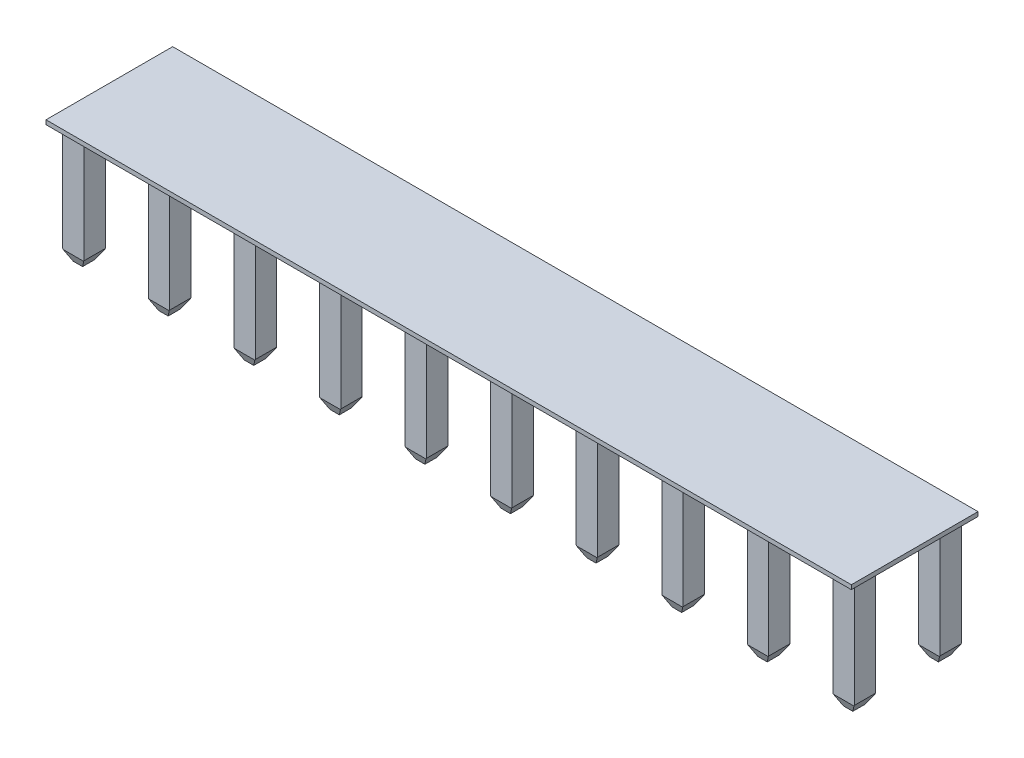
SolidWorks part; units mm, degrees
material "Pure Gold"
ref_plane "Front Plane" through (0, 0, 0) normal (0, 0, 1) x (1, 0, 0)
ref_plane "Top Plane" through (0, 0, 0) normal (0, 1, 0) x (1, 0, 0)
ref_plane "Right Plane" through (0, 0, 0) normal (1, 0, 0) x (0, 0, -1)
ref_plane "Plane1" through (0, 3.5306, 0) normal (0, -1, 0) x (1, 0, 0)
sketch "Sketch1" plane through (0, 3.5306, 0) normal (0, -1, 0) x (1, 0, 0)
  line L0 (-11.9507, 1.8796) -> (-11.9507, -1.8796)
  line L1 (-11.9507, -1.8796) -> (11.9507, -1.8796)
  line L2 (11.9507, -1.8796) -> (11.9507, 1.8796)
  line L3 (11.9507, 1.8796) -> (-11.9507, 1.8796)
extrude "Boss-Extrude1" add sketch "Sketch1" against normal blind 0.127
sketch "Sketch2" plane through (0, 3.5306, 0) normal (0, -1, 0) x (1, 0, 0)
  line L0 (11.7475, 0.9525) -> (11.1125, 0.9525)
  line L1 (11.1125, 0.9525) -> (11.1125, 1.5875)
  line L2 (11.1125, 1.5875) -> (11.7475, 1.5875)
  line L3 (11.7475, 1.5875) -> (11.7475, 0.9525)
extrude "Boss-Extrude2" add sketch "Sketch2" along normal blind 3.5306
sketch "Sketch3" plane through (0, 3.5306, 0) normal (0, -1, 0) x (1, 0, 0)
  line L0 (9.2075, 0.9525) -> (8.5725, 0.9525)
  line L1 (8.5725, 0.9525) -> (8.5725, 1.5875)
  line L2 (8.5725, 1.5875) -> (9.2075, 1.5875)
  line L3 (9.2075, 1.5875) -> (9.2075, 0.9525)
extrude "Boss-Extrude3" add sketch "Sketch3" along normal blind 3.5306
sketch "Sketch4" plane through (0, 3.5306, 0) normal (0, -1, 0) x (1, 0, 0)
  line L0 (6.6675, 0.9525) -> (6.0325, 0.9525)
  line L1 (6.0325, 0.9525) -> (6.0325, 1.5875)
  line L2 (6.0325, 1.5875) -> (6.6675, 1.5875)
  line L3 (6.6675, 1.5875) -> (6.6675, 0.9525)
extrude "Boss-Extrude4" add sketch "Sketch4" along normal blind 3.5306
sketch "Sketch5" plane through (0, 3.5306, 0) normal (0, -1, 0) x (1, 0, 0)
  line L0 (4.1275, 0.9525) -> (3.4925, 0.9525)
  line L1 (3.4925, 0.9525) -> (3.4925, 1.5875)
  line L2 (3.4925, 1.5875) -> (4.1275, 1.5875)
  line L3 (4.1275, 1.5875) -> (4.1275, 0.9525)
extrude "Boss-Extrude5" add sketch "Sketch5" along normal blind 3.5306
sketch "Sketch6" plane through (0, 3.5306, 0) normal (0, -1, 0) x (1, 0, 0)
  line L0 (1.5875, 0.9525) -> (0.9525, 0.9525)
  line L1 (0.9525, 0.9525) -> (0.9525, 1.5875)
  line L2 (0.9525, 1.5875) -> (1.5875, 1.5875)
  line L3 (1.5875, 1.5875) -> (1.5875, 0.9525)
extrude "Boss-Extrude6" add sketch "Sketch6" along normal blind 3.5306
sketch "Sketch7" plane through (0, 3.5306, 0) normal (0, -1, 0) x (1, 0, 0)
  line L0 (-0.9525, 0.9525) -> (-1.5875, 0.9525)
  line L1 (-1.5875, 0.9525) -> (-1.5875, 1.5875)
  line L2 (-1.5875, 1.5875) -> (-0.9525, 1.5875)
  line L3 (-0.9525, 1.5875) -> (-0.9525, 0.9525)
extrude "Boss-Extrude7" add sketch "Sketch7" along normal blind 3.5306
sketch "Sketch8" plane through (0, 3.5306, 0) normal (0, -1, 0) x (1, 0, 0)
  line L0 (-3.4925, 0.9525) -> (-4.1275, 0.9525)
  line L1 (-4.1275, 0.9525) -> (-4.1275, 1.5875)
  line L2 (-4.1275, 1.5875) -> (-3.4925, 1.5875)
  line L3 (-3.4925, 1.5875) -> (-3.4925, 0.9525)
extrude "Boss-Extrude8" add sketch "Sketch8" along normal blind 3.5306
sketch "Sketch9" plane through (0, 3.5306, 0) normal (0, -1, 0) x (1, 0, 0)
  line L0 (-6.0325, 0.9525) -> (-6.6675, 0.9525)
  line L1 (-6.6675, 0.9525) -> (-6.6675, 1.5875)
  line L2 (-6.6675, 1.5875) -> (-6.0325, 1.5875)
  line L3 (-6.0325, 1.5875) -> (-6.0325, 0.9525)
extrude "Boss-Extrude9" add sketch "Sketch9" along normal blind 3.5306
sketch "Sketch10" plane through (0, 3.5306, 0) normal (0, -1, 0) x (1, 0, 0)
  line L0 (-8.5725, 0.9525) -> (-9.2075, 0.9525)
  line L1 (-9.2075, 0.9525) -> (-9.2075, 1.5875)
  line L2 (-9.2075, 1.5875) -> (-8.5725, 1.5875)
  line L3 (-8.5725, 1.5875) -> (-8.5725, 0.9525)
extrude "Boss-Extrude10" add sketch "Sketch10" along normal blind 3.5306
sketch "Sketch11" plane through (0, 3.5306, 0) normal (0, -1, 0) x (1, 0, 0)
  line L0 (-11.7475, 1.5875) -> (-11.1125, 1.5875)
  line L1 (-11.1125, 1.5875) -> (-11.1125, 0.9525)
  line L2 (-11.1125, 0.9525) -> (-11.7475, 0.9525)
  line L3 (-11.7475, 0.9525) -> (-11.7475, 1.5875)
extrude "Boss-Extrude11" add sketch "Sketch11" along normal blind 3.5306
sketch "Sketch12" plane through (0, 3.5306, 0) normal (0, -1, 0) x (1, 0, 0)
  line L0 (11.7475, -1.5875) -> (11.1125, -1.5875)
  line L1 (11.1125, -1.5875) -> (11.1125, -0.9525)
  line L2 (11.1125, -0.9525) -> (11.7475, -0.9525)
  line L3 (11.7475, -0.9525) -> (11.7475, -1.5875)
extrude "Boss-Extrude12" add sketch "Sketch12" along normal blind 3.5306
sketch "Sketch13" plane through (0, 3.5306, 0) normal (0, -1, 0) x (1, 0, 0)
  line L0 (9.2075, -1.5875) -> (8.5725, -1.5875)
  line L1 (8.5725, -1.5875) -> (8.5725, -0.9525)
  line L2 (8.5725, -0.9525) -> (9.2075, -0.9525)
  line L3 (9.2075, -0.9525) -> (9.2075, -1.5875)
extrude "Boss-Extrude13" add sketch "Sketch13" along normal blind 3.5306
sketch "Sketch14" plane through (0, 3.5306, 0) normal (0, -1, 0) x (1, 0, 0)
  line L0 (6.6675, -1.5875) -> (6.0325, -1.5875)
  line L1 (6.0325, -1.5875) -> (6.0325, -0.9525)
  line L2 (6.0325, -0.9525) -> (6.6675, -0.9525)
  line L3 (6.6675, -0.9525) -> (6.6675, -1.5875)
extrude "Boss-Extrude14" add sketch "Sketch14" along normal blind 3.5306
sketch "Sketch15" plane through (0, 3.5306, 0) normal (0, -1, 0) x (1, 0, 0)
  line L0 (4.1275, -1.5875) -> (3.4925, -1.5875)
  line L1 (3.4925, -1.5875) -> (3.4925, -0.9525)
  line L2 (3.4925, -0.9525) -> (4.1275, -0.9525)
  line L3 (4.1275, -0.9525) -> (4.1275, -1.5875)
extrude "Boss-Extrude15" add sketch "Sketch15" along normal blind 3.5306
sketch "Sketch16" plane through (0, 3.5306, 0) normal (0, -1, 0) x (1, 0, 0)
  line L0 (1.5875, -1.5875) -> (0.9525, -1.5875)
  line L1 (0.9525, -1.5875) -> (0.9525, -0.9525)
  line L2 (0.9525, -0.9525) -> (1.5875, -0.9525)
  line L3 (1.5875, -0.9525) -> (1.5875, -1.5875)
extrude "Boss-Extrude16" add sketch "Sketch16" along normal blind 3.5306
sketch "Sketch17" plane through (0, 3.5306, 0) normal (0, -1, 0) x (1, 0, 0)
  line L0 (-0.9525, -1.5875) -> (-1.5875, -1.5875)
  line L1 (-1.5875, -1.5875) -> (-1.5875, -0.9525)
  line L2 (-1.5875, -0.9525) -> (-0.9525, -0.9525)
  line L3 (-0.9525, -0.9525) -> (-0.9525, -1.5875)
extrude "Boss-Extrude17" add sketch "Sketch17" along normal blind 3.5306
sketch "Sketch18" plane through (0, 3.5306, 0) normal (0, -1, 0) x (1, 0, 0)
  line L0 (-3.4925, -1.5875) -> (-4.1275, -1.5875)
  line L1 (-4.1275, -1.5875) -> (-4.1275, -0.9525)
  line L2 (-4.1275, -0.9525) -> (-3.4925, -0.9525)
  line L3 (-3.4925, -0.9525) -> (-3.4925, -1.5875)
extrude "Boss-Extrude18" add sketch "Sketch18" along normal blind 3.5306
sketch "Sketch19" plane through (0, 3.5306, 0) normal (0, -1, 0) x (1, 0, 0)
  line L0 (-6.0325, -1.5875) -> (-6.6675, -1.5875)
  line L1 (-6.6675, -1.5875) -> (-6.6675, -0.9525)
  line L2 (-6.6675, -0.9525) -> (-6.0325, -0.9525)
  line L3 (-6.0325, -0.9525) -> (-6.0325, -1.5875)
extrude "Boss-Extrude19" add sketch "Sketch19" along normal blind 3.5306
sketch "Sketch20" plane through (0, 3.5306, 0) normal (0, -1, 0) x (1, 0, 0)
  line L0 (-8.5725, -1.5875) -> (-9.2075, -1.5875)
  line L1 (-9.2075, -1.5875) -> (-9.2075, -0.9525)
  line L2 (-9.2075, -0.9525) -> (-8.5725, -0.9525)
  line L3 (-8.5725, -0.9525) -> (-8.5725, -1.5875)
extrude "Boss-Extrude20" add sketch "Sketch20" along normal blind 3.5306
sketch "Sketch21" plane through (0, 3.5306, 0) normal (0, -1, 0) x (1, 0, 0)
  line L0 (-11.7475, -0.9525) -> (-11.1125, -0.9525)
  line L1 (-11.1125, -0.9525) -> (-11.1125, -1.5875)
  line L2 (-11.1125, -1.5875) -> (-11.7475, -1.5875)
  line L3 (-11.7475, -1.5875) -> (-11.7475, -0.9525)
extrude "Boss-Extrude21" add sketch "Sketch21" along normal blind 3.5306
chamfer "Chamfer1" distance 0.308 angle 30 1 edges at (11.7475, 0, 1.27)
chamfer "Chamfer2" distance 0.308 angle 30 1 edges at (9.2075, 0, 1.27)
chamfer "Chamfer3" distance 0.308 angle 30 1 edges at (6.6675, 0, 1.27)
chamfer "Chamfer4" distance 0.308 angle 30 1 edges at (4.1275, 0, 1.27)
chamfer "Chamfer5" distance 0.308 angle 30 1 edges at (1.5875, 0, 1.27)
chamfer "Chamfer6" distance 0.308 angle 30 1 edges at (-0.9525, 0, 1.27)
chamfer "Chamfer7" distance 0.308 angle 30 1 edges at (-3.4925, 0, 1.27)
chamfer "Chamfer8" distance 0.308 angle 30 1 edges at (-6.0325, 0, 1.27)
chamfer "Chamfer9" distance 0.308 angle 30 1 edges at (-8.5725, 0, 1.27)
chamfer "Chamfer10" distance 0.308 angle 30 1 edges at (-11.1125, 0, 1.27)
chamfer "Chamfer11" distance 0.1778 angle 60 1 edges at (11.1125, 0, 1.27)
chamfer "Chamfer12" distance 0.1778 angle 60 1 edges at (8.5725, 0, 1.27)
chamfer "Chamfer13" distance 0.1778 angle 60 1 edges at (6.0325, 0, 1.27)
chamfer "Chamfer14" distance 0.1778 angle 60 1 edges at (3.4925, 0, 1.27)
chamfer "Chamfer15" distance 0.1778 angle 60 1 edges at (0.9525, 0, 1.27)
chamfer "Chamfer16" distance 0.1778 angle 60 1 edges at (-1.5875, 0, 1.27)
chamfer "Chamfer17" distance 0.1778 angle 60 1 edges at (-4.1275, 0, 1.27)
chamfer "Chamfer18" distance 0.1778 angle 60 1 edges at (-6.6675, 0, 1.27)
chamfer "Chamfer19" distance 0.1778 angle 60 1 edges at (-9.2075, 0, 1.27)
chamfer "Chamfer20" distance 0.1778 angle 60 1 edges at (-11.7475, 0, 1.27)
chamfer "Chamfer21" distance 0.1778 angle 60 1 edges at (11.7475, 0, -1.27)
chamfer "Chamfer22" distance 0.1778 angle 60 1 edges at (9.2075, 0, -1.27)
chamfer "Chamfer23" distance 0.1778 angle 60 1 edges at (6.6675, 0, -1.27)
chamfer "Chamfer24" distance 0.1778 angle 60 1 edges at (4.1275, 0, -1.27)
chamfer "Chamfer25" distance 0.1778 angle 60 1 edges at (1.5875, 0, -1.27)
chamfer "Chamfer26" distance 0.1778 angle 60 1 edges at (-0.9525, 0, -1.27)
chamfer "Chamfer27" distance 0.1778 angle 60 1 edges at (-3.4925, 0, -1.27)
chamfer "Chamfer28" distance 0.1778 angle 60 1 edges at (-6.0325, 0, -1.27)
chamfer "Chamfer29" distance 0.1778 angle 60 1 edges at (-8.5725, 0, -1.27)
chamfer "Chamfer30" distance 0.1778 angle 60 1 edges at (-11.1125, 0, -1.27)
chamfer "Chamfer31" distance 0.308 angle 30 1 edges at (11.1125, 0, -1.27)
chamfer "Chamfer32" distance 0.308 angle 30 1 edges at (8.5725, 0, -1.27)
chamfer "Chamfer33" distance 0.308 angle 30 1 edges at (6.0325, 0, -1.27)
chamfer "Chamfer34" distance 0.308 angle 30 1 edges at (3.4925, 0, -1.27)
chamfer "Chamfer35" distance 0.308 angle 30 1 edges at (0.9525, 0, -1.27)
chamfer "Chamfer36" distance 0.308 angle 30 1 edges at (-1.5875, 0, -1.27)
chamfer "Chamfer37" distance 0.308 angle 30 1 edges at (-4.1275, 0, -1.27)
chamfer "Chamfer38" distance 0.308 angle 30 1 edges at (-6.6675, 0, -1.27)
chamfer "Chamfer39" distance 0.308 angle 30 1 edges at (-9.2075, 0, -1.27)
chamfer "Chamfer40" distance 0.308 angle 30 1 edges at (-11.7475, 0, -1.27)
chamfer "Chamfer41" distance 0.1334 angle 65 1 edges at (11.43, 0, -0.9525)
chamfer "Chamfer42" distance 0.1334 angle 65 1 edges at (8.89, 0, -0.9525)
chamfer "Chamfer43" distance 0.1334 angle 65 1 edges at (6.35, 0, -0.9525)
chamfer "Chamfer44" distance 0.1334 angle 65 1 edges at (3.81, 0, -0.9525)
chamfer "Chamfer45" distance 0.1334 angle 65 1 edges at (1.27, 0, -0.9525)
chamfer "Chamfer46" distance 0.1334 angle 65 1 edges at (-1.27, 0, -0.9525)
chamfer "Chamfer47" distance 0.1334 angle 65 1 edges at (-3.81, 0, -0.9525)
chamfer "Chamfer48" distance 0.1334 angle 65 1 edges at (-6.35, 0, -0.9525)
chamfer "Chamfer49" distance 0.1334 angle 65 1 edges at (-8.89, 0, -0.9525)
chamfer "Chamfer50" distance 0.286 angle 25 1 edges at (-11.43, 0, -0.9525)
chamfer "Chamfer51" distance 0.1333 angle 65 1 edges at (-11.43, 0, -1.5875)
chamfer "Chamfer52" distance 0.1333 angle 65 1 edges at (11.43, 0, 1.5875)
chamfer "Chamfer53" distance 0.1333 angle 65 1 edges at (8.89, 0, 1.5875)
chamfer "Chamfer54" distance 0.1333 angle 65 1 edges at (6.35, 0, 1.5875)
chamfer "Chamfer55" distance 0.1333 angle 65 1 edges at (3.81, 0, 1.5875)
chamfer "Chamfer56" distance 0.1333 angle 65 1 edges at (1.27, 0, 1.5875)
chamfer "Chamfer57" distance 0.1333 angle 65 1 edges at (-1.27, 0, 1.5875)
chamfer "Chamfer58" distance 0.1333 angle 65 1 edges at (-3.81, 0, 1.5875)
chamfer "Chamfer59" distance 0.1333 angle 65 1 edges at (-6.35, 0, 1.5875)
chamfer "Chamfer60" distance 0.1333 angle 65 1 edges at (-8.89, 0, 1.5875)
chamfer "Chamfer61" distance 0.286 angle 25 1 edges at (-11.43, 0, 1.5875)
chamfer "Chamfer62" distance 0.286 angle 25 1 edges at (11.43, 0, 0.9525)
chamfer "Chamfer63" distance 0.286 angle 25 1 edges at (8.89, 0, 0.9525)
chamfer "Chamfer64" distance 0.286 angle 25 1 edges at (6.35, 0, 0.9525)
chamfer "Chamfer65" distance 0.286 angle 25 1 edges at (3.81, 0, 0.9525)
chamfer "Chamfer66" distance 0.286 angle 25 1 edges at (1.27, 0, 0.9525)
chamfer "Chamfer67" distance 0.286 angle 25 1 edges at (-1.27, 0, 0.9525)
chamfer "Chamfer68" distance 0.286 angle 25 1 edges at (-3.81, 0, 0.9525)
chamfer "Chamfer69" distance 0.286 angle 25 1 edges at (-6.35, 0, 0.9525)
chamfer "Chamfer70" distance 0.286 angle 25 1 edges at (-8.89, 0, 0.9525)
chamfer "Chamfer71" distance 0.1334 angle 65 1 edges at (-11.43, 0, 0.9525)
chamfer "Chamfer72" distance 0.286 angle 25 1 edges at (11.43, 0, -1.5875)
chamfer "Chamfer73" distance 0.286 angle 25 1 edges at (8.89, 0, -1.5875)
chamfer "Chamfer74" distance 0.286 angle 25 1 edges at (6.35, 0, -1.5875)
chamfer "Chamfer75" distance 0.286 angle 25 1 edges at (3.81, 0, -1.5875)
chamfer "Chamfer76" distance 0.286 angle 25 1 edges at (1.27, 0, -1.5875)
chamfer "Chamfer77" distance 0.286 angle 25 1 edges at (-1.27, 0, -1.5875)
chamfer "Chamfer78" distance 0.286 angle 25 1 edges at (-3.81, 0, -1.5875)
chamfer "Chamfer79" distance 0.286 angle 25 1 edges at (-6.35, 0, -1.5875)
chamfer "Chamfer80" distance 0.286 angle 25 1 edges at (-8.89, 0, -1.5875)
ref_plane "Plane2" through (11.43, 0, 0) normal (1, 0, 0) x (0, 0, -1)
sketch "Sketch22" plane through (11.43, 0, 0) normal (1, 0, 0) x (0, 0, -1)
  line L0 (-1.5875, 0.308) -> (-0.9525, 0.308) construction
  line L1 (-1.5875, 0.308) -> (-0.9525, 0.308) construction
  line L2 (-1.27, -999.692) -> (-1.27, 49000.308) construction
  point P5 (-1.27, 0.308)
